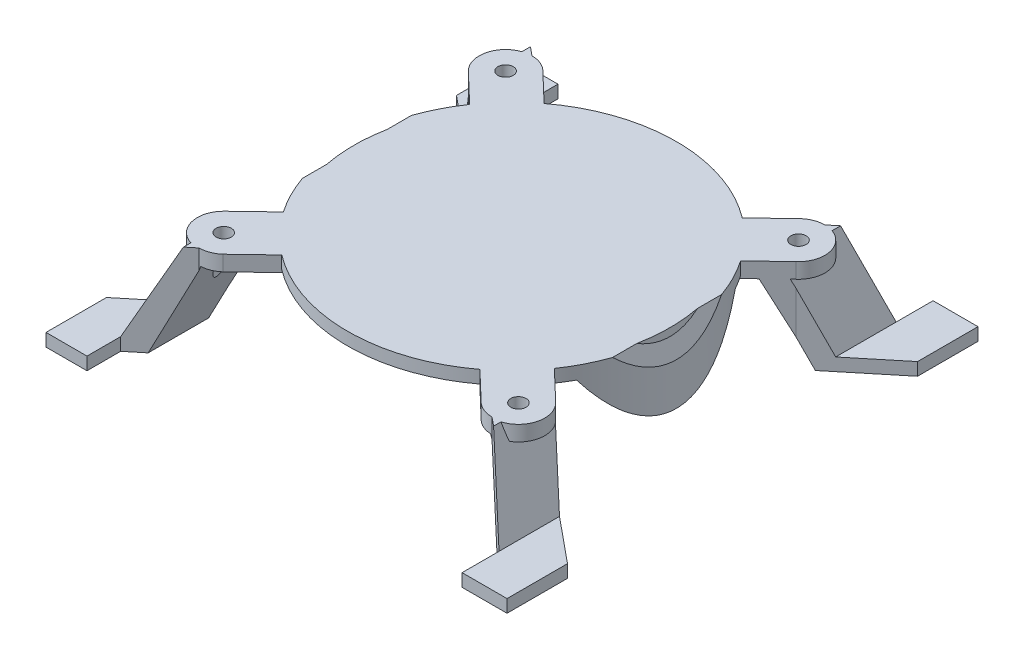
SolidWorks part; units mm, degrees
ref_plane "Front Plane" through (0, 0, 0) normal (0, 0, 1) x (1, 0, 0)
ref_plane "Top Plane" through (0, 0, 0) normal (0, 1, 0) x (1, 0, 0)
ref_plane "Right Plane" through (0, 0, 0) normal (1, 0, 0) x (0, 0, -1)
sketch "Sketch1" plane through (0, 0, 0) normal (0, 0, 1) x (1, 0, 0)
  line L0 (-52.775, -9.1598) -> (-41.775, -9.1598)
  line L1 (-41.775, -9.1598) -> (-35.7896, 6.6598)
  line L2 (-35.7896, 6.6598) -> (20.6841, 6.6598)
  line L3 (-52.775, -9.1598) -> (-52.775, -6.6598)
  line L4 (-52.775, -6.6598) -> (-44.7357, -6.6598)
  line L5 (37.6694, -6.6598) -> (28.8576, -6.6598)
  line L6 (-44.7357, -6.6598) -> (-37.9778, 9.1598)
  line L7 (-37.9778, 9.1598) -> (22.8722, 9.1598)
  line L8 (-41.775, -9.1598) -> (26.6694, -9.1598) construction
  line L9 (-7.5528, -9.1598) -> (-7.5528, 9.1598) construction
  line L10 (37.6694, -9.1598) -> (37.6694, -6.6598)
  line L11 (37.6694, -9.1598) -> (26.6694, -9.1598)
  line L13 (28.8576, -6.6598) -> (22.8722, 9.1598)
  line L14 (26.6694, -9.1598) -> (20.6841, 6.6598)
  point P8 (30.326, -6.6598)
  point P15 (-7.5528, 6.6598)
  dimension "D1" = 2.5
  dimension "D2" = 2.5
  dimension "D3" = 11
extrude "Boss-Extrude1" add sketch "Sketch1" along normal blind 92.4
sketch "Sketch2" plane through (0, 9.1598, 0) normal (0, 1, 0) x (1, 0, 0)
  line L0 (-7.5528, 0) -> (-7.5528, -92.4) construction
  line L1 (22.8722, 0) -> (-37.9778, 0) construction
  line L2 (22.8722, -92.4) -> (-37.9778, -92.4) construction
  line L3 (-32.8915, -77.579) -> (-26.0735, -71.0593)
  line L4 (10.9679, -71.0593) -> (17.7859, -77.579)
  line L5 (24.9275, -70.1107) -> (18.1095, -63.591)
  line L6 (18.1095, -28.809) -> (24.5712, -22.63)
  line L7 (17.7859, -14.821) -> (10.9679, -21.3407)
  line L8 (-26.0735, -21.3407) -> (-32.8915, -14.821)
  line L9 (-39.6768, -22.63) -> (-33.2151, -28.809)
  line L10 (-33.2151, -63.591) -> (-40.0331, -70.1107)
  arc A0 (-40.0331, -70.1107) -> (-32.8915, -77.579) centre (-36.4623, -73.8449) ccw
  arc A1 (-26.0735, -71.0593) -> (10.9679, -71.0593) centre (-7.5528, -46.2) ccw
  arc A2 (17.7859, -77.579) -> (24.9275, -70.1107) centre (21.3567, -73.8449) ccw
  arc A3 (18.1095, -63.591) -> (18.1095, -28.809) centre (-7.5528, -46.2) ccw
  arc A4 (24.5712, -22.63) -> (17.7859, -14.821) centre (21.1786, -18.7255) ccw
  arc A5 (10.9679, -21.3407) -> (-26.0735, -21.3407) centre (-7.5528, -46.2) ccw
  arc A6 (-32.8915, -14.821) -> (-39.6768, -22.63) centre (-36.2842, -18.7255) ccw
  arc A7 (-33.2151, -28.809) -> (-33.2151, -63.591) centre (-7.5528, -46.2) ccw
extrude "Boss-Extrude2" add sketch "Sketch2" against normal blind 3
sketch "Sketch3" plane through (0, 9.1598, 0) normal (0, 1, 0) x (1, 0, 0)
  circle A0 centre (-36.2842, -18.7255) radius 1.5
  circle A1 centre (21.1786, -18.7255) radius 1.5
  circle A2 centre (-36.4623, -73.8449) radius 1.5
  circle A3 centre (21.3567, -73.8449) radius 1.5
extrude "Cut-Extrude1" cut sketch "Sketch3" against normal through all
sketch "Sketch4" plane through (0, 9.1598, 0) normal (0, 1, 0) x (1, 0, 0)
  line L0 (-44.7357, -6.6071) -> (-36.2842, -13.5529)
  line L1 (-32.8915, -14.821) -> (-26.9902, -20.4641)
  line L2 (-7.5528, -13.9487) -> (-7.5528, 0) construction
  line L3 (22.8722, 0) -> (-37.9778, 0) construction
  line L4 (28.8576, -7.242) -> (21.1786, -13.5529)
  line L5 (17.7859, -14.821) -> (11.8846, -20.4641)
  line L6 (-44.7357, 0) -> (28.8576, 0)
  line L7 (-52.775, -46.2) -> (37.6694, -46.2) construction
  line L8 (-52.775, -92.4) -> (-52.775, 0) construction
  line L9 (37.6694, -92.4) -> (37.6694, 0) construction
  line L10 (28.8576, -85.158) -> (21.1786, -78.8471)
  line L11 (17.7859, -77.579) -> (11.8846, -71.9359)
  line L12 (-32.8915, -77.579) -> (-26.9902, -71.9359)
  line L13 (-44.7357, -85.7929) -> (-36.2842, -78.8471)
  line L14 (-44.7357, -92.4) -> (28.8576, -92.4)
  line L15 (-39.6768, -22.63) -> (-52.775, -11.8653)
  line L16 (-39.6768, -22.63) -> (-34.1318, -27.9324)
  line L17 (-39.6768, -69.77) -> (-34.1318, -64.4676)
  line L18 (-39.6768, -69.77) -> (-52.775, -80.5347)
  line L19 (-52.775, -11.8653) -> (-52.775, -80.5347)
  line L20 (24.5712, -69.77) -> (37.6694, -80.5347)
  line L21 (24.5712, -69.77) -> (19.0262, -64.4676)
  line L22 (24.5712, -22.63) -> (19.0262, -27.9324)
  line L23 (37.6694, -11.8653) -> (37.6694, -80.5347)
  line L24 (24.5712, -22.63) -> (37.6694, -11.8653)
  line L25 (-44.7357, -6.6071) -> (-44.7357, 0)
  line L26 (-44.7357, -92.4) -> (-44.7357, 0) construction
  line L27 (28.8576, -7.242) -> (28.8576, 0)
  line L28 (28.8576, -92.4) -> (28.8576, 0) construction
  line L29 (28.8576, -85.158) -> (28.8576, -92.4)
  line L30 (-44.7357, -92.4) -> (-44.7357, -85.7929)
  arc A0 (-32.8915, -14.821) -> (-39.6768, -22.63) centre (-36.2842, -18.7255) ccw construction
  arc A1 (-36.2842, -13.5529) -> (-32.8915, -14.821) centre (-36.2842, -18.7255) cw
  arc A2 (-26.9902, -20.4641) -> (11.8846, -20.4641) centre (-7.5528, -46.2) cw
  arc A4 (21.1786, -13.5529) -> (17.7859, -14.821) centre (21.1786, -18.7255) ccw
  arc A5 (21.1786, -78.8471) -> (17.7859, -77.579) centre (21.1786, -73.6745) cw
  arc A6 (-26.9902, -71.9359) -> (11.8846, -71.9359) centre (-7.5528, -46.2) ccw
  arc A7 (-36.2842, -78.8471) -> (-32.8915, -77.579) centre (-36.2842, -73.6745) ccw
  arc A8 (-34.1318, -27.9324) -> (-34.1318, -64.4676) centre (-7.5528, -46.2) ccw
  arc A9 (19.0262, -27.9324) -> (19.0262, -64.4676) centre (-7.5528, -46.2) cw
extrude "Cut-Extrude2" cut sketch "Sketch4" against normal through all
